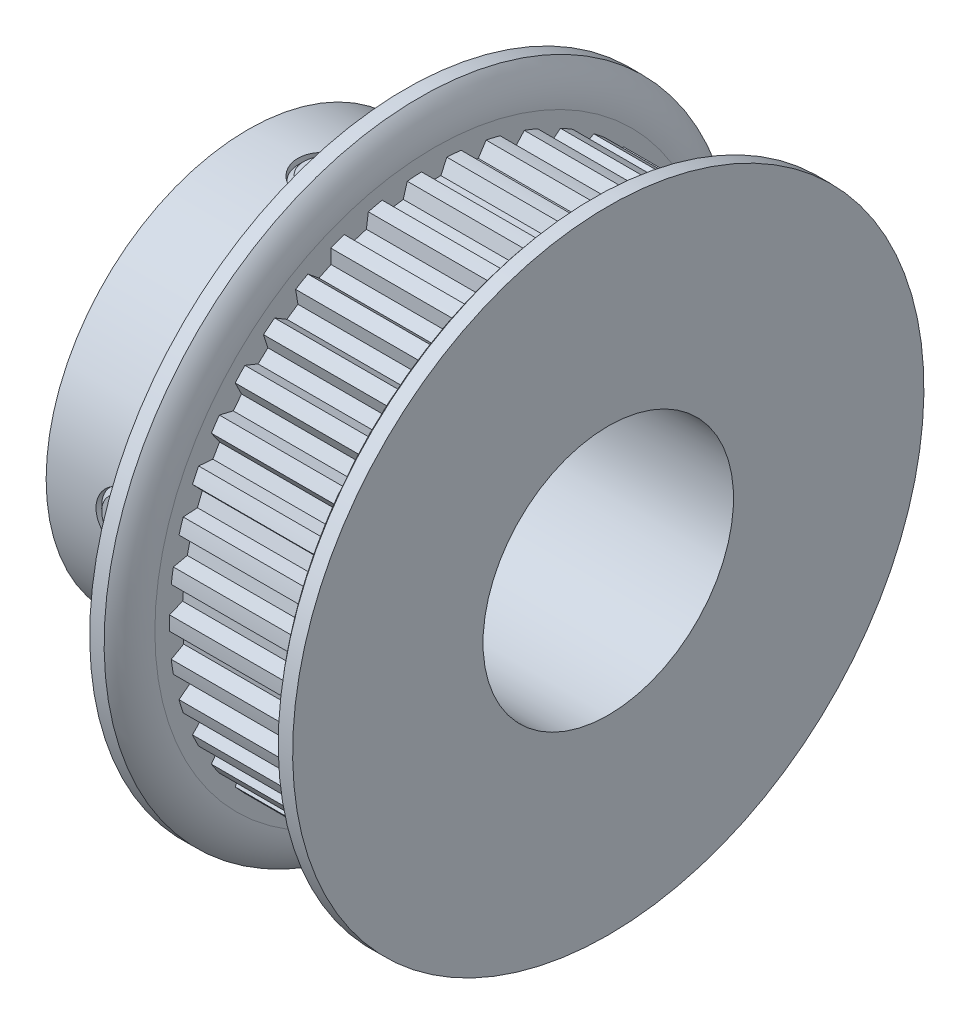
SolidWorks part; units mm, degrees
ref_plane "Front Plane" through (0, 0, 0) normal (0, 0, 1) x (1, 0, 0)
ref_plane "Top Plane" through (0, 0, 0) normal (0, 1, 0) x (1, 0, 0)
ref_plane "Right Plane" through (0, 0, 0) normal (1, 0, 0) x (0, 0, -1)
sketch "Sketch2" plane through (0, 0, 0) normal (1, 0, 0) x (0, 0, -1)
  line L3 (0, 0) -> (0, 12.7635) construction
  line L6 (0, -13.2715) -> (0, -13.589) construction
  line L7 (-0.5715, 13.2592) -> (-0.3383, 12.759)
  line L8 (0.5715, 13.2592) -> (0.3383, 12.759)
  line L9 (-0.5715, 13.2592) -> (-0.6441, 13.4148)
  line L10 (0.5715, 13.2592) -> (0.6441, 13.4148)
  line L12 (-0.3383, 12.759) -> (0.3383, 12.759)
  line L14 (0, 13.2715) -> (0, 13.589) construction
  line L15 (0, 0) -> (0, -1.143) construction
  circle A0 centre (0, 0) radius 13.589 construction
  circle A1 centre (0, 0) radius 12.7635 construction
  circle A2 centre (0, 0) radius 13.2715 construction
  arc A7 (0.6441, 13.4148) -> (-0.6441, 13.4148) centre (0, 0) ccw
  point P5 (0, 13.4303)
  dimension "D3" = 0.3175
  dimension "D1" = 50
sketch "Sketch1" plane through (0, 0, 0) normal (0, 0, 1) x (1, 0, 0)
  line L0 (-9.1313, 0) -> (9.1313, 0) construction
  line L1 (-9.1313, 6.35) -> (9.1313, 6.35)
  line L2 (-9.1313, 6.35) -> (-9.1313, 10.2362)
  line L3 (-1.1557, 16.002) -> (-0.4254, 16.002)
  line L4 (0.3048, 13.589) -> (0.3048, 14.1605)
  line L5 (0.3048, 14.732) -> (0.3048, 13.589) construction
  line L6 (0.3048, 13.589) -> (7.6708, 13.589)
  line L7 (7.6708, 13.589) -> (7.6708, 14.1605)
  line L8 (7.6708, 13.589) -> (9.1313, 13.589) construction
  line L9 (8.4011, 16.002) -> (9.1313, 16.002)
  line L10 (9.1313, 16.002) -> (9.1313, 6.35)
  line L11 (8.4011, 13.589) -> (8.4011, 16.002) construction
  line L12 (-5.1435, 10.2362) -> (-5.1435, 6.35) construction
  line L13 (-1.1557, 16.002) -> (-1.1557, 10.2362)
  line L14 (-1.1557, 10.2362) -> (-9.1313, 10.2362)
  arc A0 (7.6708, 14.1605) -> (8.4011, 16.002) centre (10.3578, 14.1605) cw
  arc A1 (0.3048, 14.1605) -> (-0.4254, 16.002) centre (-2.3822, 14.1605) ccw
  dimension "Bore Size" = 12.7
  dimension "Overall Width" = 18.2626
  dimension "Inside Width" = 7.366
  dimension "OD" = 32.004
  dimension "D2" = 27.178
  dimension "D3" = 1.143
  dimension "D4" = 0.5715
  dimension "Outside Width" = 10.287
revolve "Revolve1" add sketch "Sketch1" angle 360 mid plane about L0
sketch "Sketch4" plane through (0.3048, 0, 0) normal (1, 0, 0) x (0, 0, -1)
  circle A0 centre (0, 0) radius 13.4303
  circle A2 centre (0, 0) radius 13.589
  circle A3 centre (0, 0) radius 13.589 construction
extrude "Cut-Extrude2" cut sketch "Sketch4" along normal up to surface (7.366 mm away) up to face at (7.6708, -13.589, 0)
sketch "Sketch3" plane through (0.3048, 0, 0) normal (1, 0, 0) x (0, 0, -1)
  line L2 (-0.5715, 13.2592) -> (-0.3383, 12.759) construction
  line L3 (-0.3383, 12.759) -> (0.3383, 12.759) construction
  line L4 (0.5715, 13.2592) -> (0.3383, 12.759) construction
  line L5 (-0.6441, 13.4148) -> (-0.3383, 12.759)
  line L6 (-0.3383, 12.759) -> (0.3383, 12.759)
  line L7 (0.6441, 13.4148) -> (0.3383, 12.759)
  arc A1 (0.6441, 13.4148) -> (-0.6441, 13.4148) centre (0, 0) ccw construction
  arc A2 (0.6441, 13.4148) -> (-0.6441, 13.4148) centre (0, 0) ccw
extrude "Cut-Extrude1" cut sketch "Sketch3" along normal up to surface (7.366 mm away) up to face at (7.6708, -14.1605, 0)
pattern_circular "CirPattern1" count 42 over 360 about axis through (0, 0, 0) along (1, 0, 0) of "Cut-Extrude1"
sketch "Sketch5" plane through (0, 0, 0) normal (0, 0, 1) x (1, 0, 0)
  line L1 (7.6708, 14.1605) -> (7.6708, -14.1605) construction
  point P0 (7.6708, 0)
sketch "Sketch6" plane through (0, 0, 0) normal (0, 1, 0) x (1, 0, 0)
  line L0 (-9.1313, 0) -> (-6.604, 0) construction
  line L1 (-9.1313, 16.002) -> (-9.1313, -16.002) construction
  line L2 (-1.1557, 0) -> (-3.683, 0) construction
  line L4 (-1.1557, 16.002) -> (-1.1557, -16.002) construction
  circle A0 centre (-5.1435, 0) radius 1.4605
  dimension "D1" = 2.921
extrude "Cut-Extrude3" cut sketch "Sketch6" along normal through all
sketch "Sketch7" plane through (0, 0, 0) normal (0, 0, 1) x (1, 0, 0)
  line L0 (-6.3119, 10.2362) -> (-5.1435, 10.2362)
  line L1 (-6.5659, 9.9822) -> (-6.5659, 6.985)
  line L2 (-6.5659, 6.985) -> (-6.3119, 6.731)
  line L3 (-6.3119, 6.731) -> (-5.1435, 6.731)
  line L4 (-5.1435, 6.731) -> (-5.1435, 10.2362) construction
  line L5 (-1.1557, 10.2362) -> (-9.1313, 10.2362) construction
  line L6 (-6.5659, 9.9822) -> (-6.3119, 10.2362)
  line L8 (-5.1435, 10.2362) -> (-5.1435, 6.731)
  point P0 (-6.5659, 10.2362)
  point P4 (-6.5659, 6.731)
  dimension "D1" = 2.8448
  dimension "D2" = 0.381
revolve "Revolve2" add sketch "Sketch7" angle 360 mid plane about L4
sketch "Sketch8" plane through (0, 10.2362, 0) normal (0, 1, 0) x (1, 0, 0)
  line L1 (-5.1435, 0.8212) -> (-5.8547, 0.4106)
  line L2 (-5.8547, 0.4106) -> (-5.8547, -0.4106)
  line L3 (-5.8547, -0.4106) -> (-5.1435, -0.8212)
  line L4 (-5.1435, -0.8212) -> (-4.4323, -0.4106)
  line L5 (-4.4323, -0.4106) -> (-4.4323, 0.4106)
  line L6 (-4.4323, 0.4106) -> (-5.1435, 0.8212)
  circle A0 centre (-5.1435, 0) radius 0.7112 construction
  dimension "D1" = 1.4224
extrude "Cut-Extrude4" cut sketch "Sketch8" against normal blind 1.016
pattern_circular "CirPattern2" count 2 over 90 about axis through (-9.1313, 0, 0) along (-1, 0, 0) of "Cut-Extrude3"
pattern_circular "CirPattern3" count 2 over 90 about axis through (0, 0, 0) along (1, 0, 0) of bodies 107
sketch "Sketch9" plane through (-9.1313, 0, 0) normal (-1, 0, 0) x (0, 0, 1)
  circle A0 centre (0, 0) radius 6.35
extrude "Cut-Extrude5" [suppressed] cut sketch "Sketch9" against normal through all
equation "\"D3@Sketch2\" = (\"hs@Sketch2\"-\"ht@Sketch2\")/2"
equation "\"D2@Sketch1\" = \"PD@Sketch2\""
equation "\"D3@Sketch1\" = \"hs@Sketch2\""
equation "\"D4@Sketch1\" = \"D3@Sketch1\"/2"
